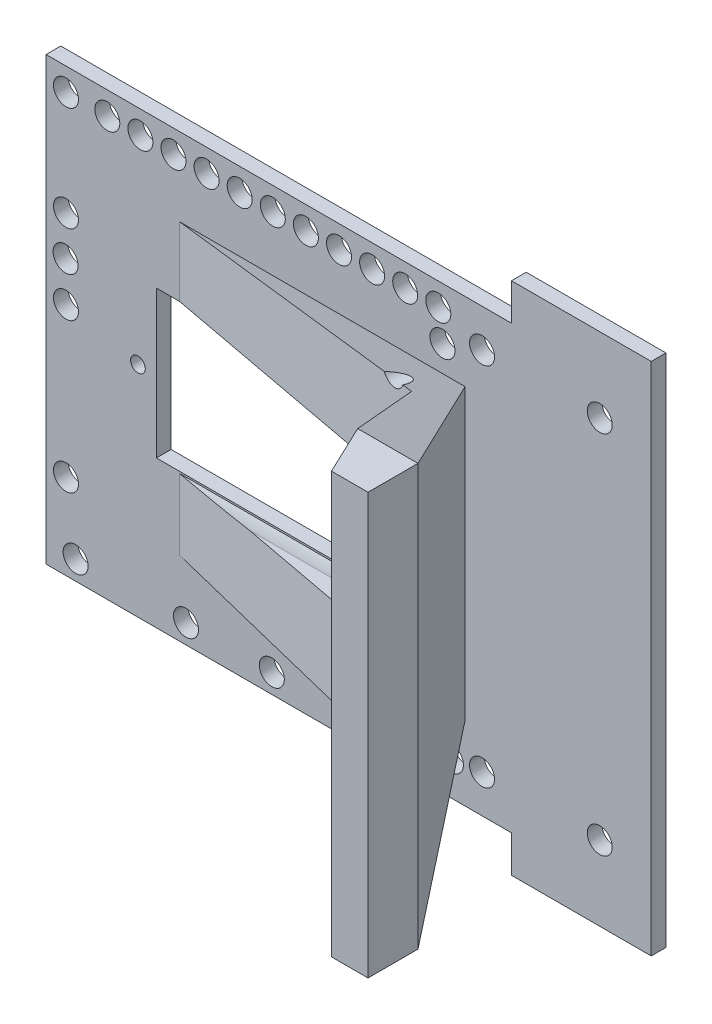
SolidWorks part; units mm, degrees
ref_plane "Plan de face" through (0, 0, 0) normal (0, 0, 1) x (1, 0, 0)
ref_plane "Plan de dessus" through (0, 0, 0) normal (0, 1, 0) x (1, 0, 0)
ref_plane "Plan de droite" through (0, 0, 0) normal (1, 0, 0) x (0, 0, -1)
sketch "Esquisse1" plane through (0, 0, 0) normal (0, 0, 1) x (1, 0, 0)
  line L0 (7, 10.15) -> (7, -59.85)
  line L1 (0, 0) -> (0, -49.7) construction
  line L2 (7, -24.85) -> (-3.4703, -24.85) construction
  line L3 (0, -24.85) -> (-8.0205, -24.85) construction
  line L4 (-12, 10.15) -> (-12, -59.85) construction
  line L5 (7, 10.15) -> (-12, 10.15)
  line L6 (-12, 10.15) -> (-12, -59.85)
  line L7 (-12, -59.85) -> (7, -59.85)
  circle A0 centre (0, 0) radius 1.7
  circle A1 centre (0, -49.7) radius 1.7
  dimension "D1" = 49.7
  dimension "D2" = 7
  dimension "D3" = 70
  dimension "D4" = 0
  dimension "D5" = 12
extrude "Boss.-Extru.1" add sketch "Esquisse1" along normal blind 2
sketch "Esquisse2" plane through (0, 0, 0) normal (0, 0, -1) x (-1, 0, 0)
  line L0 (12, -24.85) -> (-7, -24.85) construction
  line L1 (12, 10.15) -> (12, -59.85) construction
  line L2 (-7, -59.85) -> (-7, 10.15) construction
  line L7 (10.2685, 5.15) -> (75.2685, 5.15)
  line L8 (10.2685, 5.15) -> (10.2685, -54.85)
  line L9 (10.2685, -54.85) -> (75.2685, -54.85)
  line L10 (75.2685, 5.15) -> (75.2685, -54.85)
  point P19 (2.5, -24.85)
  dimension "D2" = 65
extrude "Boss.-Extru.2" add sketch "Esquisse2" against normal blind 2
sketch "Esquisse3" plane through (0, 0, 0) normal (0, 0, -1) x (-1, 0, 0)
  line L0 (25.4801, -52.2363) -> (25.4801, 5.15) construction
  line L1 (72.5629, 2.0532) -> (13.9069, 2.0532) construction
  line L3 (19.6772, -25.0949) -> (66.6772, -25.0949) construction
  line L4 (19.6772, -42.5949) -> (66.6772, -42.5949) construction
  line L5 (19.6772, -42.5949) -> (19.6772, -7.5949) construction
  line L6 (19.6772, -7.5949) -> (66.6772, -7.5949) construction
  line L7 (66.6772, -42.5949) -> (66.6772, -7.5949) construction
  line L8 (72.5629, -54.85) -> (72.5629, 5.15) construction
  line L9 (25.4801, -52.2363) -> (83.8594, -52.2363) construction
  circle A0 centre (56.248, -52.2363) radius 1.7
  circle A1 centre (25.4801, -25.0949) radius 1
  circle A2 centre (62.7801, -25.0949) radius 1
  circle A3 centre (71.248, -52.2363) radius 1.7
  circle A4 centre (21.9457, 2.0532) radius 1.7
  circle A5 centre (26.4457, 2.0532) radius 1.7
  circle A6 centre (30.9457, 2.0532) radius 1.7
  circle A7 centre (35.4457, 2.0532) radius 1.7
  circle A8 centre (72.5629, -43.2468) radius 1.7
  circle A9 centre (72.5629, -22.9468) radius 1.7
  circle A10 centre (72.5629, -12.1468) radius 1.7
  circle A11 centre (72.5629, 2.0532) radius 1.7
  circle A12 centre (25.4801, -52.2363) radius 1.7
  circle A13 centre (44.5801, -52.2363) radius 1.7
  circle A14 centre (39.9457, 2.0532) radius 1.7
  circle A15 centre (44.4457, 2.0532) radius 1.7
  circle A16 centre (48.9457, 2.0532) radius 1.7
  circle A17 centre (53.4457, 2.0532) radius 1.7
  circle A18 centre (57.9457, 2.0532) radius 1.7
  circle A19 centre (62.4457, 2.0532) radius 1.7
  circle A20 centre (66.9457, 2.0532) radius 1.7
  dimension "D4" = 10.8
  dimension "D5" = 15
  dimension "D6" = 14.2
  dimension "D7" = 11
  dimension "D11" = 20.3
  dimension "D13" = 19.1
  dimension "D2" = 35
  dimension "D3" = 47
extrude "Enlèv. mat.-Extru.1" cut sketch "Esquisse3" against normal blind 2
sketch "Esquisse4" plane through (0, 0, 0) normal (0, 0, -1) x (-1, 0, 0)
  line L0 (0, -49.7) -> (16, -49.7) construction
  line L1 (0, 0) -> (16, 0) construction
  circle A0 centre (16, -49.7) radius 1.7
  circle A1 centre (16, 0) radius 1.7
extrude "Enlèv. mat.-Extru.2" cut sketch "Esquisse4" against normal blind 2
sketch "Esquisse5" plane through (0, 0, 0) normal (0, 0, -1) x (-1, 0, 0)
  line L0 (10.2685, 5.15) -> (75.2685, 5.15) construction
  line L1 (28.8535, -14.85) -> (60.2685, -14.85)
  line L2 (28.8535, -14.85) -> (28.8535, -34.85)
  line L3 (28.8535, -34.85) -> (60.2685, -34.85)
  line L4 (60.2685, -14.85) -> (60.2685, -34.85)
  line L5 (10.2685, -54.85) -> (75.2685, -54.85) construction
  line L6 (75.2685, 5.15) -> (75.2685, -54.85) construction
  dimension "D1" = 20
  dimension "D2" = 20
  dimension "D3" = 15
extrude "Enlèv. mat.-Extru.3" cut sketch "Esquisse5" against normal blind 10
sketch "Esquisse9" plane through (0, 0, 2) normal (0, 0, 1) x (1, 0, 0)
  line L0 (0, -62.8164) -> (0, 9.2131) construction
  line L1 (4.9008, 3.5) -> (-35.3032, 3.5) construction
  line L2 (-25.4801, -25.0949) -> (4.9008, -25.0949) construction
  line L3 (-3.5, 9.2131) -> (-3.5, -62.8164) construction
  line L4 (-3.5, -53.6898) -> (-3.5, 3.5)
  line L5 (-25.4801, -25.0949) -> (-33.8304, -25.0949) construction
  line L6 (-28.8535, 3.5) -> (-60.3467, 3.5)
  line L7 (-28.8535, -25.0949) -> (-28.8535, 3.5) construction
  line L8 (-28.8535, -34.85) -> (-28.8535, -14.85) construction
  line L9 (-3.5, 3.5) -> (-28.8535, 3.5)
  line L11 (-3.5, -53.6898) -> (-28.8535, -53.6898)
  line L12 (-60.3467, 3.5) -> (-60.3467, -53.6898)
  line L13 (-60.3467, -53.6898) -> (-28.8535, -53.6898)
  circle A0 centre (0, 0) radius 1.7 construction
  point P21 (-3.5, -25.0949)
  dimension "D1" = 3.5
  dimension "D2" = 3.5
extrude "Boss.-Extru.7" add sketch "Esquisse9" along normal blind 28
sketch "Esquisse10" plane through (0, 3.5, 0) normal (0, 1, 0) x (1, 0, 0)
  line L0 (-18.3014, -2) -> (-3.5, -2)
  line L1 (-3.5, -2) -> (-3.5, -23.2085)
  line L2 (-3.5, -30) -> (-3.5, -2) construction
  line L3 (-8.4729, -30) -> (-18.3014, -9.2742)
  line L4 (-18.3014, -2) -> (-3.5, -23.2085)
  line L5 (-18.3014, -9.2742) -> (-57.1239, -2)
  line L6 (-3.5, -30) -> (-60.3467, -30) construction
  line L7 (-8.4729, -30) -> (-28.8535, -30)
  line L8 (-28.8535, -30) -> (-60.8555, -30)
  line L9 (-60.8555, -30) -> (-60.8555, -2)
  line L10 (-75.2685, -2) -> (-12, -2) construction
  line L11 (-60.8555, -2) -> (-57.1239, -2)
extrude "Enlèv. mat.-Extru.4" cut sketch "Esquisse10" against normal blind 60
sketch "Esquisse11" plane through (7, 0, 0) normal (1, 0, 0) x (0, 0, -1)
  line L0 (-23.2085, 3.5) -> (-2, -5.4658)
  line L1 (-2, -53.6898) -> (-2, 3.5) construction
  line L2 (-2, -5.4658) -> (-2, 3.5)
  line L3 (-2, 3.5) -> (-23.2085, 3.5)
  line L4 (-30, -25.0949) -> (11.6292, -25.0949) construction
  line L5 (-30, -53.6898) -> (-30, 3.5) construction
  line L6 (-2, -44.7239) -> (-2, -53.6898)
  line L7 (-23.2085, -53.6898) -> (-2, -44.7239)
  line L8 (-2, -53.6898) -> (-23.2085, -53.6898)
extrude "Enlèv. mat.-Extru.5" cut sketch "Esquisse11" against normal blind 72
sketch "Esquisse12" plane through (7, 0, 0) normal (1, 0, 0) x (0, 0, -1)
  line L0 (-30, -25.0949) -> (6.2554, -25.0949) construction
  line L1 (-30, -53.6898) -> (-30, 3.5) construction
  line L2 (-2, -44.7239) -> (-2, -5.4658) construction
  line L3 (-9.5782, -10.7437) -> (-9.5782, -40.3957) construction
  line L5 (-2, -15.0949) -> (-2, -35.0949)
  line L6 (-9.5782, -18.5702) -> (-19.579, -25.0949)
  line L7 (-19.579, -25.0949) -> (-9.5782, -31.6195)
  arc A0 (-2, -35.0949) -> (-9.5782, -31.6195) centre (-2, -25.0949) cw
  arc A1 (-9.5782, -18.5702) -> (-2, -15.0949) centre (-2, -25.0949) cw
extrude "Enlèv. mat.-Extru.6" cut sketch "Esquisse12" against normal blind 67
sketch "Esquisse13" plane through (0, 0, 2) normal (0, 0, 1) x (1, 0, 0)
  line L0 (-60.2685, -14.85) -> (-60.2685, -34.85) construction
  line L1 (-60.2685, -14.85) -> (-22.77, -14.85)
  line L2 (-60.2685, -14.85) -> (-60.2685, -34.85)
  line L3 (-60.2685, -34.85) -> (-22.77, -34.85)
  line L4 (-22.77, -14.85) -> (-22.77, -20.893)
  line L5 (-60.2685, -34.85) -> (-28.8535, -34.85) construction
  line L6 (-22.77, -29.2967) -> (-22.77, -34.85)
  arc A0 (-22.77, -29.2967) -> (-22.77, -20.893) centre (-25.4801, -25.0949) ccw
extrude "Enlèv. mat.-Extru.7" cut sketch "Esquisse13" along normal blind 35
sketch "Esquisse14" plane through (-13.2457, 0, 9.2442) normal (0.82, 0, -0.5723) x (-0.5723, 0, -0.82)
  line L0 (8.8339, -35.0949) -> (10.1681, -35.0949)
  line L1 (8.8339, -35.0949) -> (-13.4397, -35.0949)
  line L3 (8.8339, -15.0949) -> (-13.4397, -15.0949)
  line L4 (-13.4397, -35.0949) -> (-13.4397, -15.0949)
  line L5 (10.1681, -35.0949) -> (10.1681, -15.0949)
  line L6 (10.1681, -15.0949) -> (8.8339, -15.0949)
extrude "Boss.-Extru.11" add sketch "Esquisse14" against normal blind 2
sketch "Esquisse15" plane through (0, 0, 0) normal (0, 0, -1) x (-1, 0, 0)
  circle B0 centre (20.2337, -50.1436) radius 1.7
  circle B1 centre (21.3768, -1.9436) radius 1.7
  circle B2 centre (72.6168, -17.5536) radius 1.7
sketch_block_instance "Bloc2-1"
sketch_block "Bloc2" parameters "D1"=1.143
extrude "Enlèv. mat.-Extru.8" cut sketch "Esquisse15" against normal blind 10
sketch "Esquisse16" plane through (0, 0, 0) normal (0, 0, -1) x (-1, 0, 0)
  circle A0 centre (25.4801, -52.2363) radius 1.7
  circle A1 centre (44.5801, -52.2363) radius 1.7
  circle A2 centre (56.248, -52.2363) radius 1.7
  circle A3 centre (71.248, -52.2363) radius 1.7
